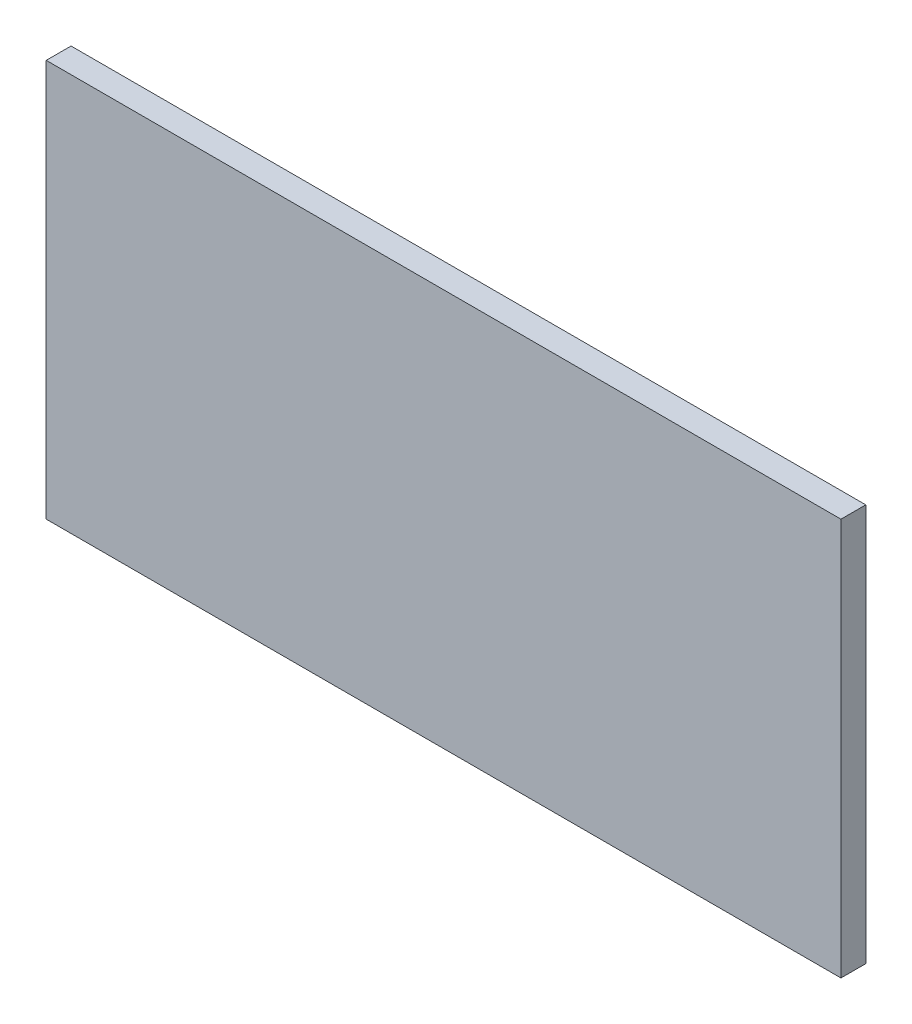
SolidWorks part; units mm, degrees
material "ASTM A36 Steel"
ref_plane "Front Plane" through (0, 0, 0) normal (0, 0, 1) x (1, 0, 0)
ref_plane "Top Plane" through (0, 0, 0) normal (0, 1, 0) x (1, 0, 0)
ref_plane "Right Plane" through (0, 0, 0) normal (1, 0, 0) x (0, 0, -1)
sketch "Sketch1" plane through (0, 0, 0) normal (0, 0, 1) x (1, 0, 0)
  line L1 (-50.8, 25.4) -> (50.8, 25.4)
  line L2 (-50.8, 25.4) -> (-50.8, -25.4)
  line L3 (-50.8, -25.4) -> (50.8, -25.4)
  line L4 (50.8, 25.4) -> (50.8, -25.4)
  line L5 (-50.8, 25.4) -> (50.8, -25.4) construction
  line L6 (-50.8, -25.4) -> (50.8, 25.4) construction
  point P0 (0, 0)
  dimension "D1" = 101.6
  dimension "D2" = 50.8
extrude "Boss-Extrude1" add sketch "Sketch1" along normal blind 3.175
